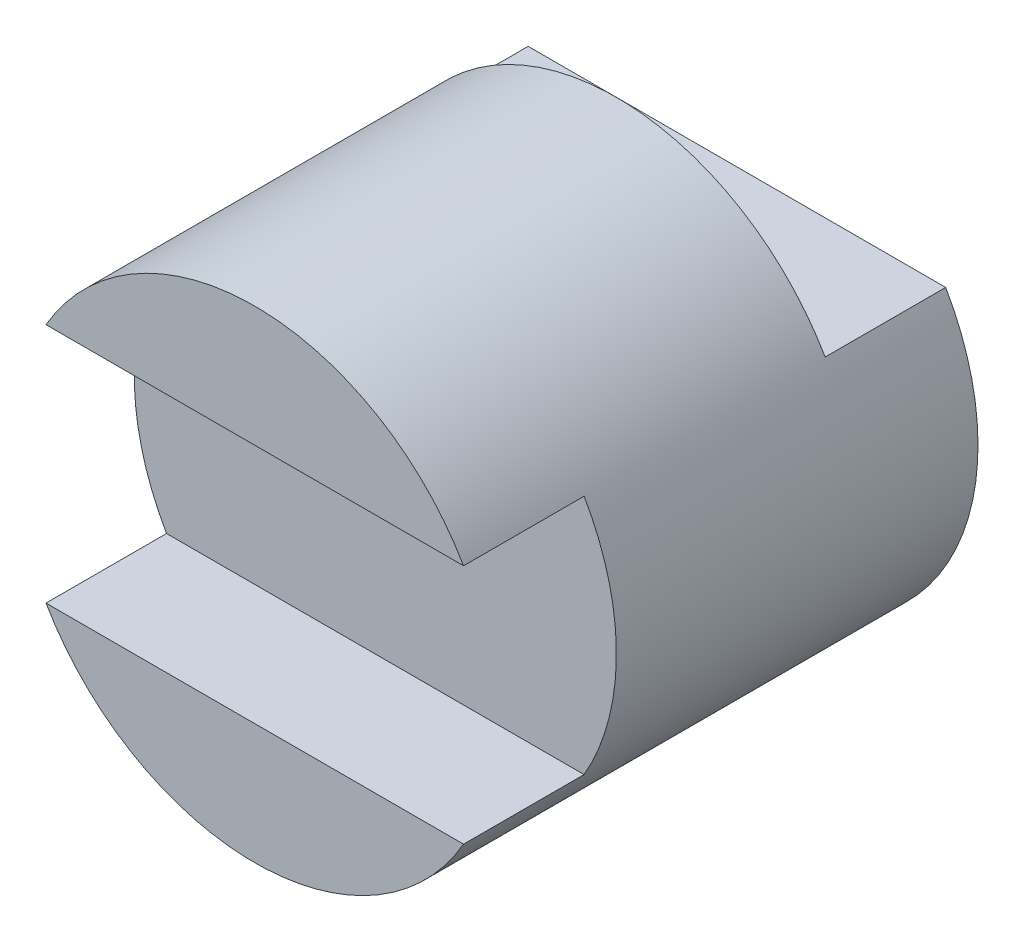
SolidWorks part; units mm, degrees
ref_plane "Front" through (0, 0, 0) normal (0, 0, 1) x (1, 0, 0)
ref_plane "Top" through (0, 0, 0) normal (0, 1, 0) x (1, 0, 0)
ref_plane "Right" through (0, 0, 0) normal (1, 0, 0) x (0, 0, -1)
sketch "Sketch1" plane through (0, 0, 0) normal (0, 0, 1) x (1, 0, 0)
  circle A0 centre (0, 0) radius 2
  dimension "D1" = 4
extrude "Boss-Extrude1" add sketch "Sketch1" along normal blind 3
sketch "Sketch2" plane through (0, 0, 3) normal (0, 0, 1) x (1, 0, 0)
  line L0 (-1.7321, 1) -> (1.7321, 1)
  circle A0 centre (0, 0) radius 2 construction
  arc A1 (-1.7321, 1) -> (1.7321, 1) centre (0, 0) cw
  dimension "D1" = 1
extrude "Boss-Extrude2" add sketch "Sketch2" along normal blind 1
sketch "Sketch3" plane through (0, 0, 0) normal (0, 0, -1) x (-1, 0, 0)
  line L0 (1.7321, 1) -> (-1.7321, 1)
  arc A0 (1.7321, 1) -> (-1.7321, 1) centre (0, 0) ccw
extrude "Cut-Extrude1" cut sketch "Sketch3" against normal blind 1
sketch "Sketch4" plane through (0, 0, 3) normal (0, 0, 1) x (1, 0, 0)
  line L0 (1.7321, -1) -> (-1.7321, -1)
  arc A0 (-1.7321, 1) -> (1.7321, 1) centre (0, 0) ccw construction
  arc A1 (-1.7321, -1) -> (1.7321, -1) centre (0, 0) ccw
  dimension "D1" = 1
extrude "Boss-Extrude3" add sketch "Sketch4" along normal blind 1
